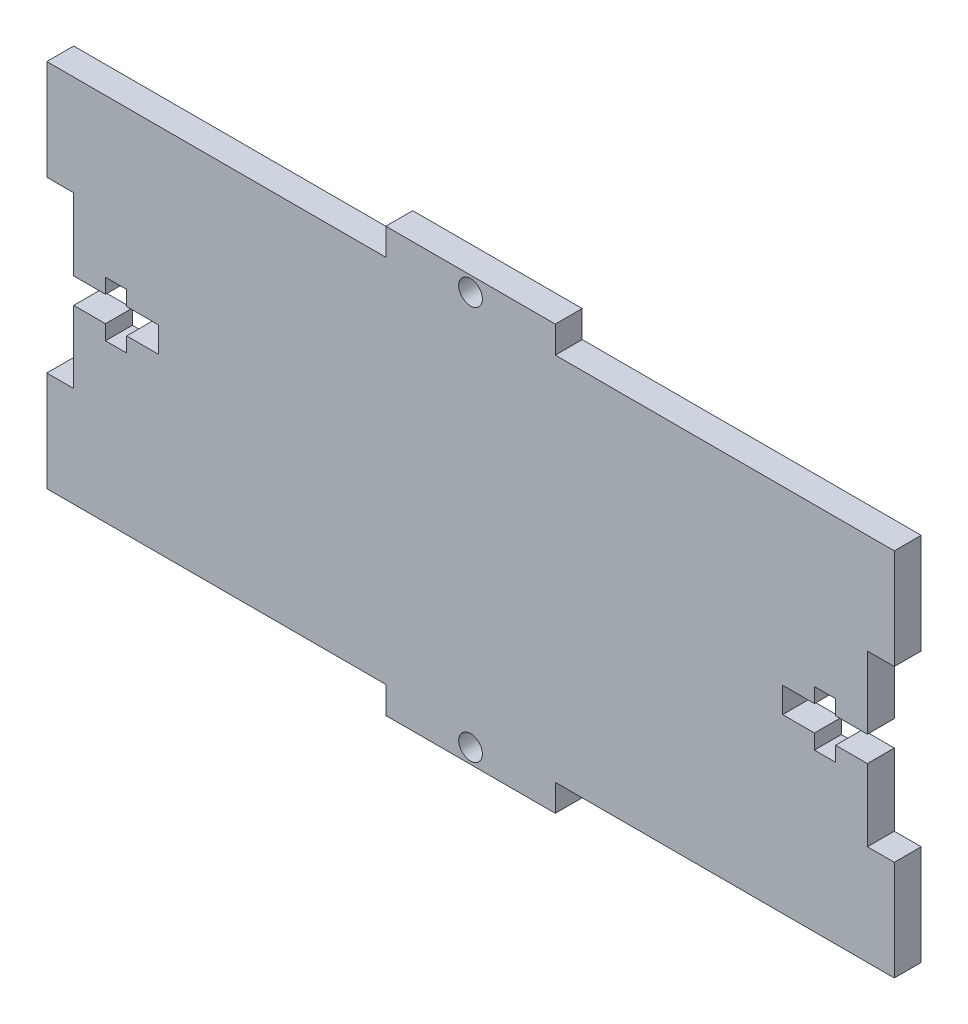
SolidWorks part; units mm, degrees
ref_plane "Front Plane" through (0, 0, 0) normal (0, 0, 1) x (1, 0, 0)
ref_plane "Top Plane" through (0, 0, 0) normal (0, 1, 0) x (1, 0, 0)
ref_plane "Right Plane" through (0, 0, 0) normal (1, 0, 0) x (0, 0, -1)
sketch "Sketch1" plane through (0, 0, 0) normal (0, 0, 1) x (1, 0, 0)
  line L1 (-50, 25) -> (50, 25)
  line L2 (-50, 25) -> (-50, -25)
  line L3 (-50, -25) -> (50, -25)
  line L4 (50, 25) -> (50, -25)
  line L5 (-50, 25) -> (50, -25) construction
  line L6 (-50, -25) -> (50, 25) construction
  point P0 (0, 0)
  dimension "D2" = 50
  dimension "D1" = 100
extrude "Boss-Extrude1" add sketch "Sketch1" along normal blind 3.175
sketch "Sketch5" plane through (-7.3885, -2.5562, 3.175) normal (0, 0, 1) x (1, 0, 0)
  line L1 (-42.6115, 24.3812) -> (-2.6115, 24.3812)
  line L2 (-42.6115, 24.3812) -> (-42.6115, 27.5562)
  line L3 (-42.6115, 27.5562) -> (-2.6115, 27.5562)
  line L4 (-2.6115, 24.3812) -> (-2.6115, 27.5562)
  line L5 (57.3885, 27.5562) -> (-42.6115, 27.5562) construction
  line L7 (57.3885, 24.3812) -> (17.3885, 24.3812)
  line L8 (57.3885, 24.3812) -> (57.3885, 27.5562)
  line L9 (57.3885, 27.5562) -> (17.3885, 27.5562)
  line L10 (17.3885, 24.3812) -> (17.3885, 27.5562)
  line L11 (7.3885, 27.5562) -> (7.3885, 4.502) construction
  circle A0 centre (7.3885, 25.8062) radius 1.4
  dimension "D2" = 2.8
  dimension "D1" = 20
  dimension "D3" = 1.75
  dimension "D4" = 3.175
extrude "Cut-Extrude1" cut sketch "Sketch5" against normal through all
other "Tab<1>"
mirror "Mirror1" about plane through (0, 0, 0) normal (0, 1, 0) of "Cut-Extrude1"
sketch "Sketch59" [suppressed] plane through (52.683, -8.9384, 3.175) normal (0, 0, 1) x (1, 0, 0)
  line L1 (44.142, 30.7634) -> (44.142, 18.9384)
  line L2 (44.142, 30.7634) -> (47.317, 30.7634)
  line L3 (47.317, 30.7634) -> (47.317, 18.9384)
  line L4 (44.142, 18.9384) -> (47.317, 18.9384)
  line L5 (47.317, -12.8866) -> (47.317, 30.7634) construction
  line L7 (44.142, -12.8866) -> (44.142, -1.0616)
  line L8 (44.142, -12.8866) -> (47.317, -12.8866)
  line L9 (47.317, -12.8866) -> (47.317, -1.0616)
  line L10 (44.142, -1.0616) -> (47.317, -1.0616)
  line L11 (47.317, 8.9384) -> (0, 8.9384) construction
  circle A0 centre (45.567, 8.9384) radius 1.4
  dimension "D2" = 2.8
  dimension "D1" = 20
  dimension "D3" = 1.75
  dimension "D4" = 3.175
extrude "Cut-Extrude19" [suppressed] cut sketch "Sketch59" against normal through all
other "Tab<2>" [suppressed]
sketch "Sketch510" [suppressed] plane through (-58.5586, -8.9971, 0) normal (0, 0, -1) x (-1, 0, 0)
  line L1 (38.2664, 30.8221) -> (38.2664, 18.9971)
  line L2 (38.2664, 30.8221) -> (41.4414, 30.8221)
  line L3 (41.4414, 30.8221) -> (41.4414, 18.9971)
  line L4 (38.2664, 18.9971) -> (41.4414, 18.9971)
  line L5 (41.4414, -12.8279) -> (41.4414, 30.8221) construction
  line L7 (38.2664, -12.8279) -> (38.2664, -1.0029)
  line L8 (38.2664, -12.8279) -> (41.4414, -12.8279)
  line L9 (41.4414, -12.8279) -> (41.4414, -1.0029)
  line L10 (38.2664, -1.0029) -> (41.4414, -1.0029)
  line L11 (41.4414, 8.9971) -> (0, 8.9971) construction
  circle A0 centre (39.6914, 8.9971) radius 1.4
  dimension "D2" = 2.8
  dimension "D1" = 20
  dimension "D3" = 1.75
  dimension "D4" = 3.175
extrude "Cut-Extrude110" [suppressed] cut sketch "Sketch510" against normal through all
other "Tab<3>" [suppressed]
sketch "Sketch3" plane through (2.4354, -11.5608, 0) normal (0, 0, -1) x (-1, 0, 0)
  line L0 (-47.5646, 33.3858) -> (-47.5646, -10.2642) construction
  line L1 (-47.5646, 1.5608) -> (-47.5646, 21.5608)
  line L2 (-47.5646, 1.5608) -> (-44.3896, 1.5608)
  line L3 (-44.3896, 1.5608) -> (-44.3896, 10.0608)
  line L4 (-47.5646, 21.5608) -> (-44.3896, 21.5608)
  line L5 (-44.3896, 10.0608) -> (-40.6396, 10.0608)
  line L6 (-40.6396, 10.0608) -> (-40.6396, 8.3108)
  line L7 (-40.6396, 8.3108) -> (-38.1396, 8.3108)
  line L8 (-38.1396, 8.3108) -> (-38.1396, 10.0608)
  line L9 (-38.1396, 10.0608) -> (-34.3896, 10.0608)
  line L10 (-34.3896, 10.0608) -> (-34.3896, 13.0608)
  line L11 (-34.3896, 13.0608) -> (-38.1396, 13.0608)
  line L12 (-38.1396, 13.0608) -> (-38.1396, 14.8108)
  line L13 (-38.1396, 14.8108) -> (-40.6396, 14.8108)
  line L14 (-40.6396, 14.8108) -> (-40.6396, 13.0608)
  line L15 (-40.6396, 13.0608) -> (-44.3896, 13.0608)
  line L16 (-47.5646, 11.5608) -> (-34.3896, 11.5608) construction
  line L17 (-44.3896, 13.0608) -> (-44.3896, 21.5608)
  point P39 (-47.5646, 11.5608)
  dimension "D1" = 3.175
  dimension "D2" = 20
  dimension "D3" = 10
  dimension "D4" = 2.5
  dimension "D5" = 1.75
  dimension "D6" = 3
extrude "T Cut" cut sketch "Sketch3" against normal through all
other "T Cut<1>"
sketch "Sketch32" plane through (-11.5423, -7.3222, 3.175) normal (0, 0, 1) x (1, 0, 0)
  line L0 (-38.4577, 29.1472) -> (-38.4577, -14.5028) construction
  line L1 (-38.4577, -2.6778) -> (-38.4577, 17.3222)
  line L2 (-38.4577, -2.6778) -> (-35.2827, -2.6778)
  line L3 (-35.2827, -2.6778) -> (-35.2827, 5.8222)
  line L4 (-38.4577, 17.3222) -> (-35.2827, 17.3222)
  line L5 (-35.2827, 5.8222) -> (-31.5327, 5.8222)
  line L6 (-31.5327, 5.8222) -> (-31.5327, 4.0722)
  line L7 (-31.5327, 4.0722) -> (-29.0327, 4.0722)
  line L8 (-29.0327, 4.0722) -> (-29.0327, 5.8222)
  line L9 (-29.0327, 5.8222) -> (-25.2827, 5.8222)
  line L10 (-25.2827, 5.8222) -> (-25.2827, 8.8222)
  line L11 (-25.2827, 8.8222) -> (-29.0327, 8.8222)
  line L12 (-29.0327, 8.8222) -> (-29.0327, 10.5722)
  line L13 (-29.0327, 10.5722) -> (-31.5327, 10.5722)
  line L14 (-31.5327, 10.5722) -> (-31.5327, 8.8222)
  line L15 (-31.5327, 8.8222) -> (-35.2827, 8.8222)
  line L16 (-38.4577, 7.3222) -> (-25.2827, 7.3222) construction
  line L17 (-35.2827, 8.8222) -> (-35.2827, 17.3222)
  point P39 (-38.4577, 7.3222)
  dimension "D1" = 3.175
  dimension "D2" = 20
  dimension "D3" = 10
  dimension "D4" = 2.5
  dimension "D5" = 1.75
  dimension "D6" = 3
extrude "T Cut2" cut sketch "Sketch32" against normal through all
other "T Cut<2>"
sketch "Sketch33" [suppressed] plane through (-8.38, 0.2655, 0) normal (0, 0, -1) x (-1, 0, 0)
  line L0 (116.62, 49.7345) -> (-133.38, 49.7345) construction
  line L1 (-18.38, 49.7345) -> (1.62, 49.7345)
  line L2 (-18.38, 49.7345) -> (-18.38, 46.5595)
  line L3 (-18.38, 46.5595) -> (-9.88, 46.5595)
  line L4 (1.62, 49.7345) -> (1.62, 46.5595)
  line L5 (-9.88, 46.5595) -> (-9.88, 42.8095)
  line L6 (-9.88, 42.8095) -> (-11.63, 42.8095)
  line L7 (-11.63, 42.8095) -> (-11.63, 40.3095)
  line L8 (-11.63, 40.3095) -> (-9.88, 40.3095)
  line L9 (-9.88, 40.3095) -> (-9.88, 36.5595)
  line L10 (-9.88, 36.5595) -> (-6.88, 36.5595)
  line L11 (-6.88, 36.5595) -> (-6.88, 40.3095)
  line L12 (-6.88, 40.3095) -> (-5.13, 40.3095)
  line L13 (-5.13, 40.3095) -> (-5.13, 42.8095)
  line L14 (-5.13, 42.8095) -> (-6.88, 42.8095)
  line L15 (-6.88, 42.8095) -> (-6.88, 46.5595)
  line L16 (-8.38, 49.7345) -> (-8.38, 36.5595) construction
  line L17 (-6.88, 46.5595) -> (1.62, 46.5595)
  point P39 (-8.38, 49.7345)
  dimension "D1" = 3.175
  dimension "D2" = 20
  dimension "D3" = 10
  dimension "D4" = 2.5
  dimension "D5" = 1.75
  dimension "D6" = 3
extrude "T Cut3" [suppressed] cut sketch "Sketch33" against normal through all
other "T Cut<3>" [suppressed]
mirror "Mirror2" [suppressed] about plane through (0, 0, 0) normal (0, 1, 0)
sketch "Sketch511" [suppressed] plane through (0, 0, 0) normal (0, 0, -1) x (-1, 0, 0)
  circle A0 centre (-15, 0) radius 3.5
  dimension "D1" = 7
  dimension "D2" = 15
extrude "Cut-Extrude111" [suppressed] cut sketch "Sketch511" against normal through all
pattern_linear "LPattern1" [suppressed] count 3 spacing 30 count 2 spacing 30
sketch "Sketch512" [suppressed] plane through (0, 0, 0) normal (0, 0, -1) x (-1, 0, 0)
  line L2 (125, 50) -> (125, 10) construction
  line L3 (10, 50) -> (125, 50) construction
  circle A0 centre (95, 25) radius 6.3
  dimension "D1" = 12.6
  dimension "D2" = 25
  dimension "D3" = 30
extrude "Cut-Extrude112" [suppressed] cut sketch "Sketch512" against normal through all
sketch "Sketch513" [suppressed] plane through (0, 0, 0) normal (0, 0, -1) x (-1, 0, 0)
  line L0 (0, 13.82) -> (0, -13.82) construction
  circle A0 centre (-25, 0) radius 6.3
  circle A1 centre (25, 0) radius 6.3
  point P4 (0, 0)
  dimension "D1" = 12.6
  dimension "D2" = 50
extrude "Cut-Extrude113" [suppressed] cut sketch "Sketch513" against normal through all
sketch "Sketch514" [suppressed] plane through (0, 0, 0) normal (0, 0, -1) x (-1, 0, 0)
  line L0 (-25, 0) -> (-25, 2.6011) construction
  line L1 (-25, 0) -> (-16, 0) construction
  circle A0 centre (-16, 0) radius 1.5
  circle A1 centre (-25, 0) radius 6.3 construction
  circle A2 centre (-25, 0) radius 6.3 construction
  circle A3 centre (-34, 0) radius 1.5
  dimension "D1" = 3
  dimension "D2" = 18
extrude "Cut-Extrude114" [suppressed] cut sketch "Sketch514" against normal through all
mirror "Mirror3" [suppressed] about plane through (0, 0, 0) normal (1, 0, 0)
equation "\"width\"= 250"
equation "\"height\"= 50"
equation "\"depth\"= 100"
equation "\"D2@Sketch1\"      = \"height\""
equation "\"D1@Sketch1\"  = \"depth\""
